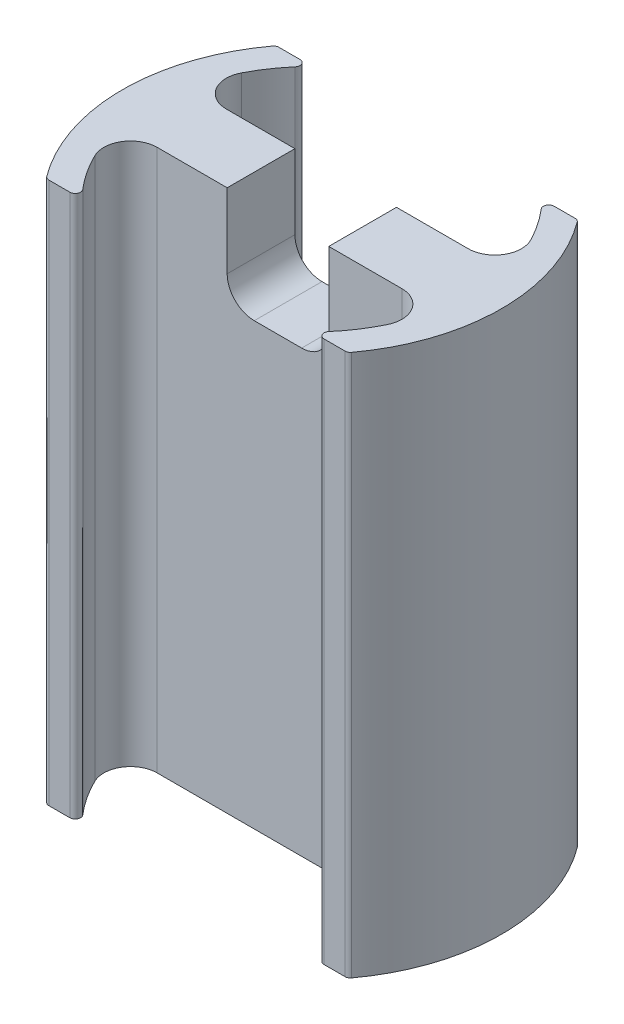
SolidWorks part; units mm, degrees
other "Markup1"
sketch "Sketch10" plane through (35.56, 101.6006, 21.5646) normal (0.0583, 0.6566, 0.752) x (0.9788, 0.1107, -0.1725)
ref_plane "Front Plane" through (0, 0, 0) normal (0, 0, 1) x (1, 0, 0)
ref_plane "Top Plane" through (0, 0, 0) normal (0, 1, 0) x (1, 0, 0)
ref_plane "Right Plane" through (0, 0, 0) normal (1, 0, 0) x (0, 0, -1)
sketch "Sketch2" plane through (0, 0, 0) normal (0, 1, 0) x (1, 0, 0)
  line L10 (-21.5406, -21.5646) -> (-28.2751, -21.5646)
  line L11 (-29.8642, -6.096) -> (29.8642, -6.096)
  line L13 (-29.756, 6.604) -> (29.756, 6.604)
  line L15 (21.5406, -21.5646) -> (28.2751, -21.5646)
  line L16 (21.5406, 21.5646) -> (28.2751, 21.5646)
  line L17 (-21.5406, 21.5646) -> (-28.2751, 21.5646)
  arc A0 (-28.2751, 21.5646) -> (-28.2751, -21.5646) centre (0, 0) ccw
  arc A1 (-21.5406, 21.5646) -> (-29.756, 6.604) centre (0, 0) ccw
  arc A2 (28.2751, -21.5646) -> (28.2751, 21.5646) centre (0, 0) ccw
  arc A3 (21.5406, -21.5646) -> (29.8642, -6.096) centre (0, 0) ccw
  arc A4 (-29.8642, -6.096) -> (-21.5406, -21.5646) centre (0, 0) ccw
  arc A5 (29.756, 6.604) -> (21.5406, 21.5646) centre (0, 0) ccw
  dimension "D1" = 71.12
  dimension "D2" = 60.96
  dimension "D3" = 12.7
extrude "Boss-Extrude2" add sketch "Sketch2" along normal blind 101.6
fillet "Fillet3" radius 1 8 edges at (28.2751, 50.8, -21.5646) (21.5406, 50.8, -21.5646) (-21.5406, 50.8, -21.5646) (-28.2751, 50.8, -21.5646) (28.2751, 50.8, 21.5646) (-28.2751, 50.8, 21.5646) (21.5406, 50.8, 21.5646) (-21.5406, 50.8, 21.5646)
fillet "Fillet5" radius 5 4 edges at (29.756, 50.8, -6.604) (29.8642, 50.8, 6.096) (-29.756, 50.8, -6.604) (-29.8642, 50.8, 6.096)
sketch "Sketch8" plane through (0, 101.6, 0) normal (0, 1, 0) x (1, 0, 0)
  circle A0 centre (0, 0) radius 3.175
  dimension "D1" = 6.35
extrude "Cut-Extrude3" cut sketch "Sketch8" against normal blind 19.05
sketch "Sketch9" plane through (0, 0, 6.096) normal (0, 0, 1) x (1, 0, 0)
  line L0 (-22.9371, 101.6) -> (22.9371, 101.6) construction
  line L1 (-9.8107, 82.55) -> (9.2393, 82.55)
  line L2 (-9.8107, 82.55) -> (-9.8107, 101.6)
  line L3 (-9.8107, 101.6) -> (9.2393, 101.6)
  line L4 (9.2393, 82.55) -> (9.2393, 101.6)
  line L5 (-9.8107, 82.55) -> (9.2393, 101.6) construction
  line L6 (-9.8107, 101.6) -> (9.2393, 82.55) construction
  point P0 (-0.2857, 92.075)
  dimension "D1" = 0
  dimension "D2" = 19.05
  dimension "D3" = 19.05
extrude "Cut-Extrude4" cut sketch "Sketch9" against normal up to surface (12.7 mm away) up to face at (0, 50.8, -6.604)
fillet "Fillet6" radius 5.08 2 edges at (9.2393, 82.55, -0.254) (-9.8107, 82.55, -0.254)
sketch "Sketch11" plane through (0, 0, 6.096) normal (0, 0, 1) x (1, 0, 0)
  line L0 (-22.9371, 0) -> (22.9371, 0) construction
  line L1 (8.5871, -6) -> (16.5871, -6)
  line L2 (8.5871, -6) -> (8.5871, 6)
  line L3 (8.5871, 6) -> (16.5871, 6)
  line L4 (16.5871, -6) -> (16.5871, 6)
  line L5 (8.5871, -6) -> (16.5871, 6) construction
  line L6 (8.5871, 6) -> (16.5871, -6) construction
  line L7 (22.9371, 0) -> (22.9371, 101.6) construction
  point P0 (12.5871, 0)
  dimension "D1" = 6.35
  dimension "D2" = 12
  dimension "D3" = 8
extrude "Cut-Extrude5" cut sketch "Sketch11" against normal up to surface (12.7 mm away) up to face at (-0.1714, 74.4656, -6.604)
fillet "Fillet7" radius 2.54 2 edges at (16.5871, 6, -0.254) (8.5871, 6, -0.254)
